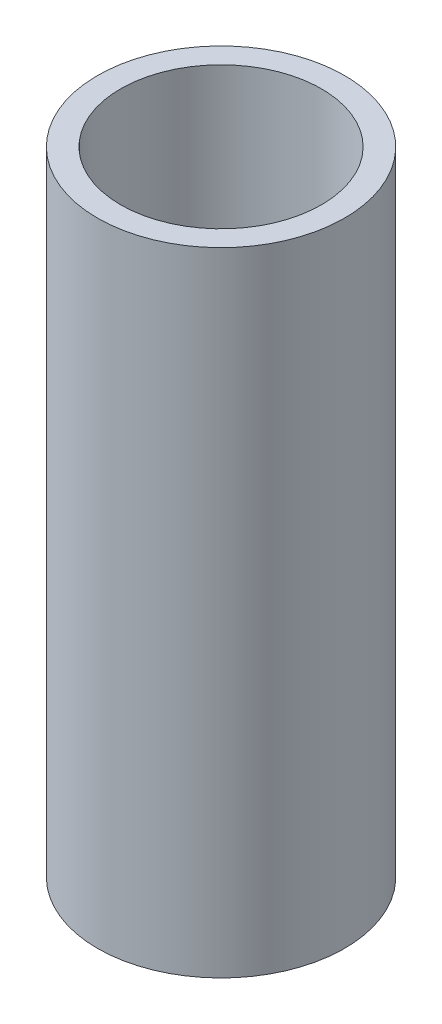
SolidWorks part; units mm, degrees
ref_plane "Front Plane" through (0, 0, 0) normal (0, 0, 1) x (1, 0, 0)
ref_plane "Top Plane" through (0, 0, 0) normal (0, 1, 0) x (1, 0, 0)
ref_plane "Right Plane" through (0, 0, 0) normal (1, 0, 0) x (0, 0, -1)
sketch "Sketch3" plane through (0, 0, 0) normal (0, 1, 0) x (1, 0, 0)
  circle A0 centre (0, 0) radius 30.5
  circle A1 centre (0, 0) radius 37.5
extrude "Boss-Extrude1" add sketch "Sketch3" along normal blind 192 contours A0 | A1
